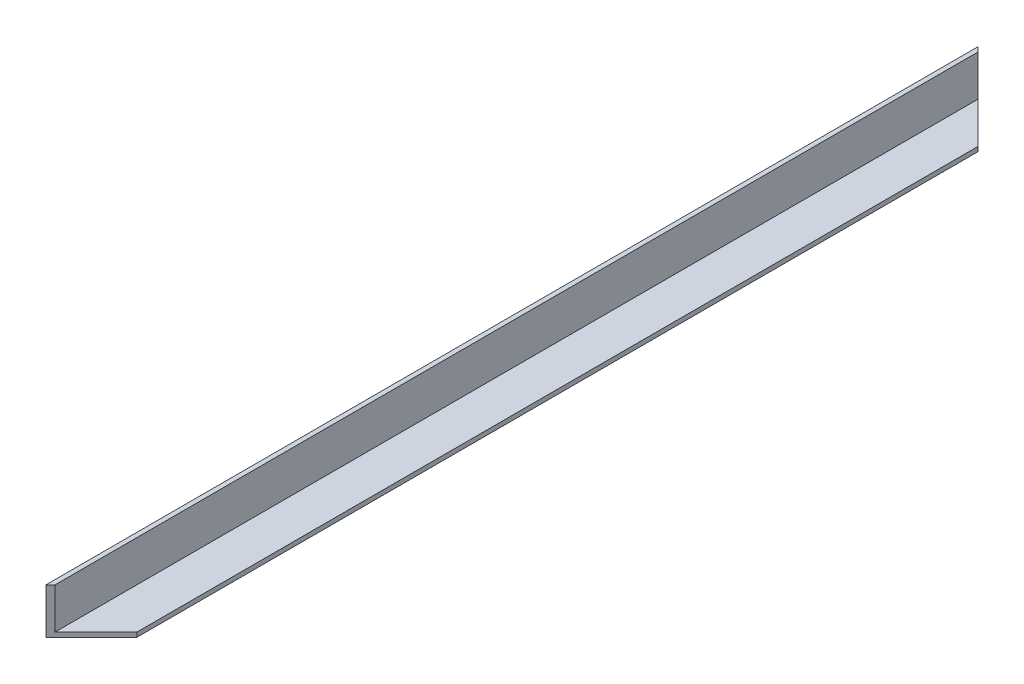
SolidWorks part; units mm, degrees
ref_plane "Front Plane" through (0, 0, 0) normal (0, 0, 1) x (1, 0, 0)
ref_plane "Top Plane" through (0, 0, 0) normal (0, 1, 0) x (1, 0, 0)
ref_plane "Right Plane" through (0, 0, 0) normal (1, 0, 0) x (0, 0, -1)
sketch "Sketch1" plane through (0, 0, 0) normal (0, 0, 1) x (1, 0, 0)
  line L0 (0, 20) -> (0, 0)
  line L1 (0, 0) -> (20, 0)
  line L2 (20, 0) -> (20, 2)
  line L3 (20, 2) -> (2, 2)
  line L4 (2, 2) -> (2, 20)
  line L5 (2, 20) -> (0, 20)
  dimension "D1" = 2
  dimension "D2" = 2
  dimension "D3" = 20
  dimension "D4" = 20
extrude "Boss-Extrude1" add sketch "Sketch1" along normal blind 410
sketch "Sketch2" plane through (0, 20, 0) normal (0, 1, 0) x (1, 0, 0)
  line L0 (0, 0) -> (20, -20)
  line L1 (20, -410) -> (20, 0) construction
  line L2 (20, -20) -> (20, 0)
  line L3 (20, 0) -> (0, 0)
  line L4 (0, -410) -> (20, -390)
  line L5 (20, -390) -> (20, -410)
  line L6 (20, -410) -> (0, -410)
extrude "Cut-Extrude1" cut sketch "Sketch2" against normal through all
